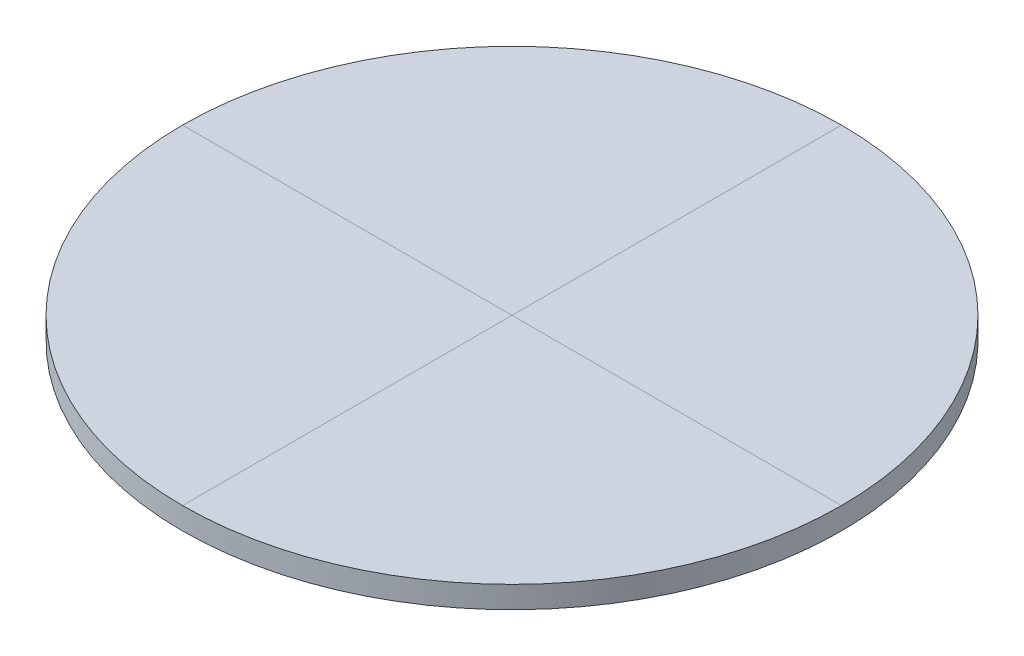
SolidWorks part; units mm, degrees
ref_plane "Front Plane" through (0, 0, 0) normal (0, 0, 1) x (1, 0, 0)
ref_plane "Top Plane" through (0, 0, 0) normal (0, 1, 0) x (1, 0, 0)
ref_plane "Right Plane" through (0, 0, 0) normal (1, 0, 0) x (0, 0, -1)
sketch "Sketch1" plane through (0, 0, 0) normal (0, 1, 0) x (1, 0, 0)
  circle A0 centre (0, 0) radius 15
  dimension "D1" = 30
extrude "Boss-Extrude1" add sketch "Sketch1" along normal blind 1
split line "Split Line1"
split line "Split Line2"
